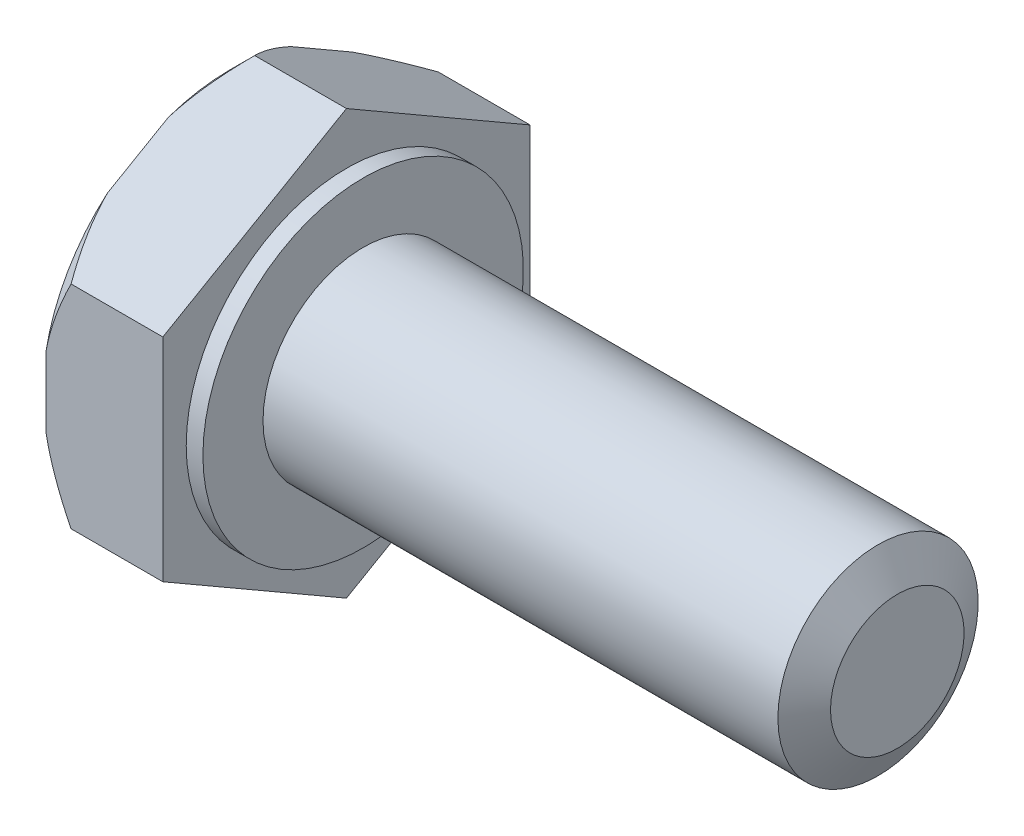
SolidWorks part; units mm, degrees
material "1.4944.4"
ref_plane "Front Plane" through (0, 0, 0) normal (0, 0, 1) x (1, 0, 0)
ref_plane "Top Plane" through (0, 0, 0) normal (0, 1, 0) x (1, 0, 0)
ref_plane "Right Plane" through (0, 0, 0) normal (1, 0, 0) x (0, 0, -1)
ref_axis "Axis1" through (-88.99, 0, 0) along (1, 0, 0)
sketch "Sketch1" plane through (0, 0, 0) normal (0, 0, 1) x (1, 0, 0)
  line L0 (0, 1.5) -> (0, 2.4)
  line L1 (0, 2.4) -> (-0.25, 2.4)
  line L2 (-0.25, 2.4) -> (-0.25, 3.3)
  line L3 (-0.25, 3.3) -> (-1.5, 3.3)
  line L4 (-2, 2.8) -> (-2, 0)
  line L5 (-88.99, 0) -> (88.99, 0) construction
  line L6 (-2, 0) -> (8, 0)
  line L7 (8, 0) -> (8, 1)
  line L8 (8, 1) -> (7.7113, 1.5)
  line L9 (7.7113, 1.5) -> (0, 1.5)
  line L10 (-1.5, 3.3) -> (-2, 2.8)
  point P6 (-2, 3.3)
  dimension "D1" = 3
  dimension "D2" = 6.6
  dimension "D3" = 2
  dimension "D4" = 0.25
  dimension "D5" = 0.5
  dimension "D6" = 30
  dimension "D7" = 8
  dimension "D8" = 0.9
  dimension "D9" = 1.8
revolve "Revolve1" add sketch "Sketch1" angle 360 about axis through (-88.99, 0, 0) along (1, 0, 0)
sketch "Sketch2" plane through (0, 0, 0) normal (1, 0, 0) x (0, 0, -1)
  line L1 (0, 3.1754) -> (-2.75, 1.5877)
  line L2 (-2.75, 1.5877) -> (-2.75, -1.5877)
  line L3 (-2.75, -1.5877) -> (0, -3.1754)
  line L4 (0, -3.1754) -> (2.75, -1.5877)
  line L5 (2.75, -1.5877) -> (2.75, 1.5877)
  line L6 (2.75, 1.5877) -> (0, 3.1754)
  circle A0 centre (0, 0) radius 2.75 construction
  dimension "D1" = 5.5
extrude "Cut-Extrude1" cut sketch "Sketch2" against normal blind 10 flip side to cut
equation "\"M\"=3"
equation "\"k\"= 2"
equation "\"s\"= 5.5"
equation "\"L\"= 8"
equation "\"D1@Sketch1\"=\"M\""
equation "\"D2@Sketch1\"=\"s\"*1.2"
equation "\"D3@Sketch1\"=\"k\""
equation "\"D7@Sketch1\"=\"L\""
equation "\"D8@Sketch1\"=\"D9@Sketch1\"/2"
equation "\"D1@Sketch2\"=\"s\""
